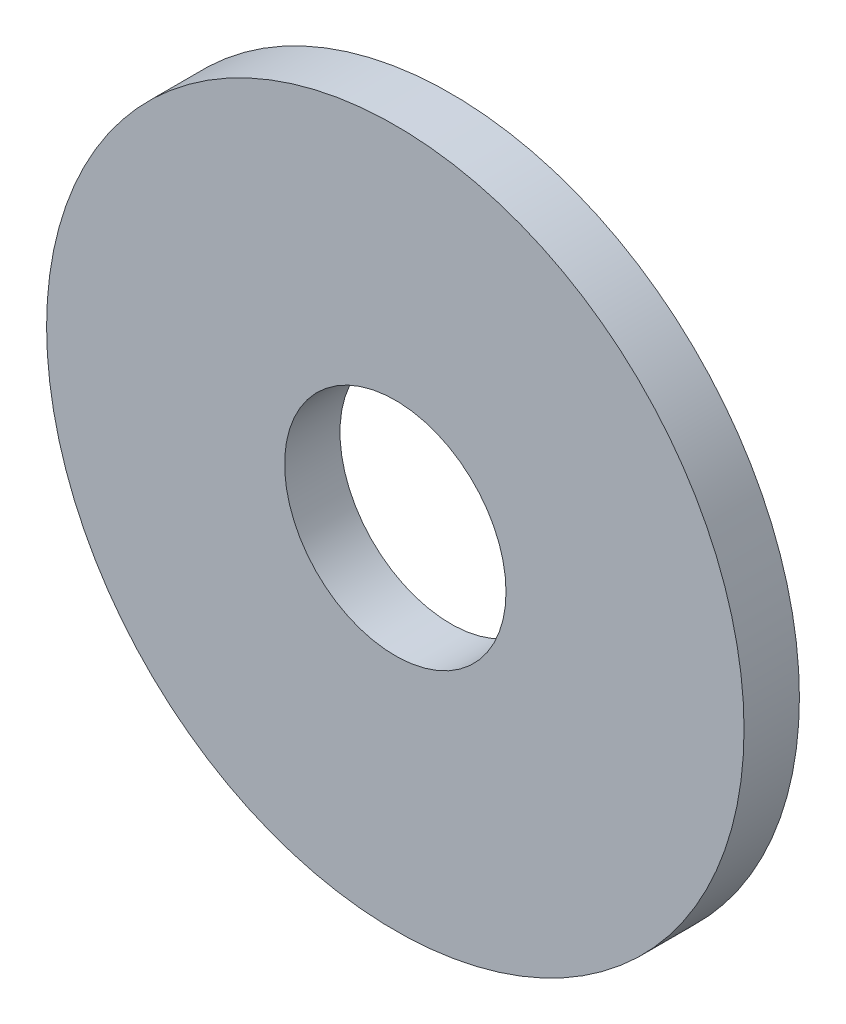
SolidWorks part; units mm, degrees
ref_plane "Front Plane" through (0, 0, 0) normal (0, 0, 1) x (1, 0, 0)
ref_plane "Top Plane" through (0, 0, 0) normal (0, 1, 0) x (1, 0, 0)
ref_plane "Right Plane" through (0, 0, 0) normal (1, 0, 0) x (0, 0, -1)
sketch "Sketch1" plane through (0, 0, 0) normal (0, 0, 1) x (1, 0, 0)
  circle A0 centre (0, 0) radius 2.54
  circle A1 centre (0, 0) radius 8.001
  dimension "ID" = 5.08
  dimension "OD" = 16.002
extrude "Extrude1" add sketch "Sketch1" against normal blind 1.27
